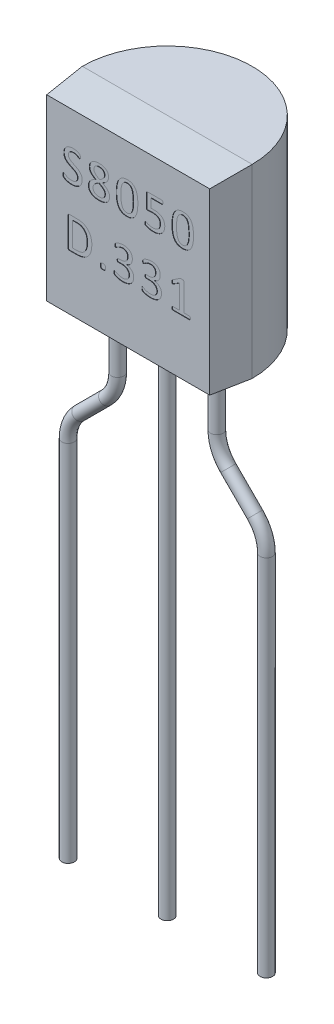
SolidWorks part; units mm, degrees
material "6061-T6 (SS)"
ref_plane "Front Plane" through (0, 0, 0) normal (0, 0, 1) x (1, 0, 0)
ref_plane "Top Plane" through (0, 0, 0) normal (0, 1, 0) x (1, 0, 0)
ref_plane "Right Plane" through (0, 0, 0) normal (1, 0, 0) x (0, 0, -1)
sketch "Sketch1" plane through (0, 0, 0) normal (0, 1, 0) x (1, 0, 0)
  line L0 (-2.175, 0) -> (2.175, 0)
  line L4 (0, 0) -> (0, -1.075) construction
  line L5 (0, 0) -> (0, 2.175) construction
  arc A0 (2.175, 0) -> (-2.175, 0) centre (0, 0) ccw
  dimension "D1" = 4.35
extrude "Boss-Extrude1" add sketch "Sketch1" along normal blind 4.75
sketch "Sketch2" plane through (0, 0, 0) normal (0, 0, 1) x (1, 0, 0)
  line L4 (-2.175, 0) -> (2.175, 0)
  line L5 (2.175, 0) -> (2.175, 4.75)
  line L6 (2.175, 4.75) -> (-2.175, 4.75)
  line L7 (-2.175, 4.75) -> (-2.175, 0)
  line L8 (-2.175, 0) -> (2.175, 0)
  line L9 (2.175, 0) -> (2.175, 4.75)
  line L10 (2.175, 4.75) -> (-2.175, 4.75)
  line L11 (-2.175, 4.75) -> (-2.175, 0)
  dimension "D1" = 0
extrude "Boss-Extrude2" add sketch "Sketch2" along normal blind 1 draft 5
sketch "Sketch3" plane through (0, 0, 1) normal (0, 0, 1) x (1, 0, 0)
  line L0 (0, 0) -> (0, 1.5) construction
  line L1 (0, 1.5) -> (0, 3) construction
  line L2 (-2.0875, 1.5) -> (2.0875, 1.5) construction
  line L3 (-2.0875, 4.6625) -> (-2.0875, 0.0875) construction
  line L4 (-2.0875, 3) -> (2.0875, 3) construction
  text T0 "S8050" font "Calibri" height 0.8
  text T1 "D.331" font "Calibri" height 0.8
  dimension "D1" = 1.5
  dimension "D2" = 3
extrude "Cut-Extrude1" cut sketch "Sketch3" against normal blind 0.01
sketch "Sketch4" plane through (0, 0, 0) normal (0, -1, 0) x (1, 0, 0)
  line L0 (-1.27, 0) -> (1.27, 0) construction
  circle A0 centre (0, 0) radius 0.16
  circle A1 centre (1.27, 0) radius 0.16
  circle A2 centre (-1.27, 0) radius 0.16
  dimension "D2" = 0.32
  dimension "D1" = 2.54
extrude "Boss-Extrude3" add sketch "Sketch4" along normal blind 1 and the other way blind 1 separate body
sketch "Sketch9" plane through (0, 0, 0) normal (0, 0, 1) x (1, 0, 0)
  line L0 (0.16, 1) -> (-0.16, 1) construction
  line L1 (-1.43, 1.5) -> (1.43, 1.5)
  line L2 (-1.43, 1.5) -> (-1.43, 0.5)
  line L3 (-1.43, 0.5) -> (1.43, 0.5)
  line L4 (1.43, 1.5) -> (1.43, 0.5)
  line L5 (-1.43, 1.5) -> (1.43, 0.5) construction
  line L6 (-1.43, 0.5) -> (1.43, 1.5) construction
  line L7 (-1.43, 1) -> (1.43, 1) construction
  point P0 (0, 1)
  dimension "D1" = 1
extrude "Boss-Extrude5" add sketch "Sketch9" along normal mid plane 0.2
sketch "Sketch6" plane through (0, -1, 0) normal (0, -1, 0) x (1, 0, 0)
  circle A1 centre (0, 0) radius 0.16
  circle A2 centre (0, 0) radius 0.16
  dimension "D1" = 0
extrude "Boss-Extrude4" add sketch "Sketch6" along normal blind 12
sketch "Sketch7" plane through (0, 0, 0) normal (0, 0, 1) x (1, 0, 0)
  line L0 (0, 0) -> (0, -13) construction
  line L1 (-0.16, -13) -> (0.16, -13) construction
  line L2 (-2.54, -13) -> (2.54, -13) construction
  line L3 (-2.54, -13) -> (-2.54, -3.6842)
  line L4 (-2.2471, -2.9771) -> (-1.5629, -2.2929)
  line L5 (-1.27, -1.5858) -> (-1.27, -1)
  line L6 (-1.43, -1) -> (-1.11, -1) construction
  line L7 (2.54, -13) -> (2.54, -3.6842) construction
  line L8 (2.2471, -2.9771) -> (1.5629, -2.2929) construction
  line L9 (1.27, -1.5858) -> (1.27, -1) construction
  line L10 (1.11, -1) -> (1.43, -1) construction
  line L11 (-1.27, -2) -> (0, -2) construction
  line L12 (0, -2) -> (1.27, -2) construction
  line L13 (-2.54, -3.27) -> (0, -3.27) construction
  line L14 (0, -3.27) -> (2.54, -3.27) construction
  arc A0 (-2.54, -3.6842) -> (-2.2471, -2.9771) centre (-1.54, -3.6842) cw
  arc A1 (-1.5629, -2.2929) -> (-1.27, -1.5858) centre (-2.27, -1.5858) ccw
  arc A2 (2.54, -3.6842) -> (2.2471, -2.9771) centre (1.54, -3.6842) ccw construction
  arc A3 (1.5629, -2.2929) -> (1.27, -1.5858) centre (2.27, -1.5858) cw construction
  dimension "D4" = 1
  dimension "D1" = 5.08
  dimension "D2" = 1
  dimension "D3" = 45
sketch "Sketch8" plane through (0, -1, 0) normal (0, -1, 0) x (1, 0, 0)
  circle A1 centre (-1.27, 0) radius 0.16
  circle A2 centre (-1.27, 0) radius 0.16
  dimension "D1" = 0
sweep "Sweep1" add profiles "Sketch8" path "Sketch7"
mirror "Mirror2" about plane through (0, 0, 0) normal (1, 0, 0) of "Sweep1"
